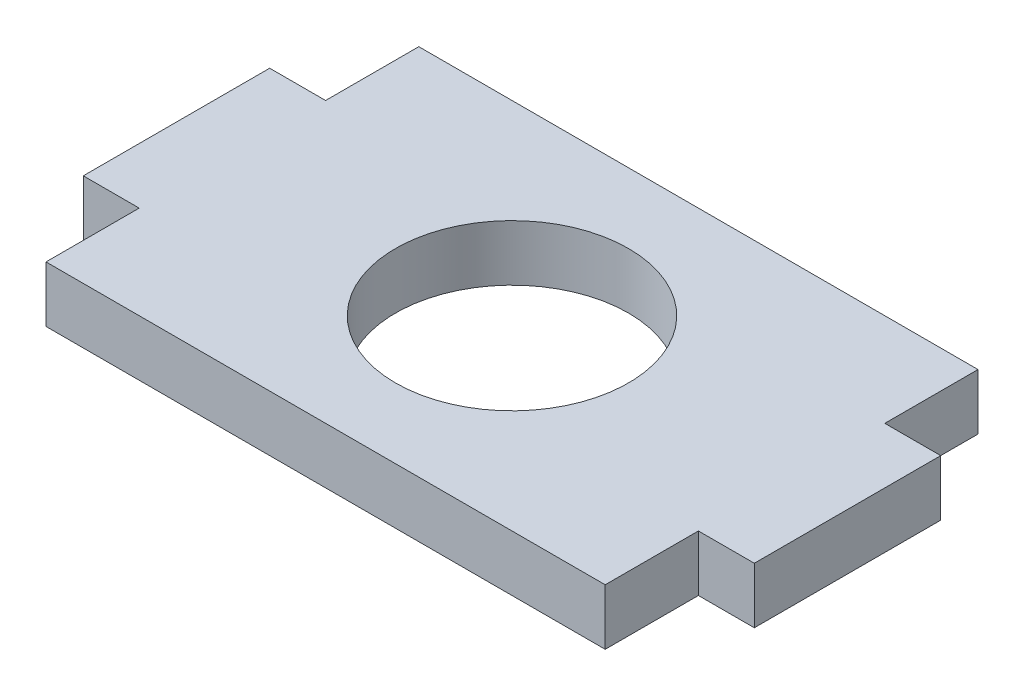
SolidWorks part; units mm, degrees
ref_plane "Front Plane" through (0, 0, 0) normal (0, 0, 1) x (1, 0, 0)
ref_plane "Top Plane" through (0, 0, 0) normal (0, 1, 0) x (1, 0, 0)
ref_plane "Right Plane" through (0, 0, 0) normal (1, 0, 0) x (0, 0, -1)
sketch "Sketch1" plane through (0, 0, 0) normal (0, 1, 0) x (1, 0, 0)
  line L0 (-15, 10) -> (-15, 5)
  line L1 (15, 10) -> (-15, 10)
  line L2 (-15, 5) -> (-18, 5)
  line L3 (15, -10) -> (-15, -10)
  line L4 (-18, 5) -> (-18, -5)
  line L5 (15, 10) -> (-15, -10) construction
  line L6 (15, -10) -> (-15, 10) construction
  line L7 (-18, -5) -> (-15, -5)
  line L8 (-15, -5) -> (-15, -10)
  line L9 (15, -10) -> (15, -5)
  line L10 (15, -5) -> (18, -5)
  line L11 (18, -5) -> (18, 5)
  line L12 (18, 5) -> (15, 5)
  line L13 (15, 5) -> (15, 10)
  circle A0 centre (0, 0) radius 6.25
  point P0 (0, 0)
  dimension "D5" = 12.5
  dimension "D1" = 30
  dimension "D2" = 20
  dimension "D3" = 5
  dimension "D4" = 3
extrude "Boss-Extrude1" add sketch "Sketch1" along normal blind 3
